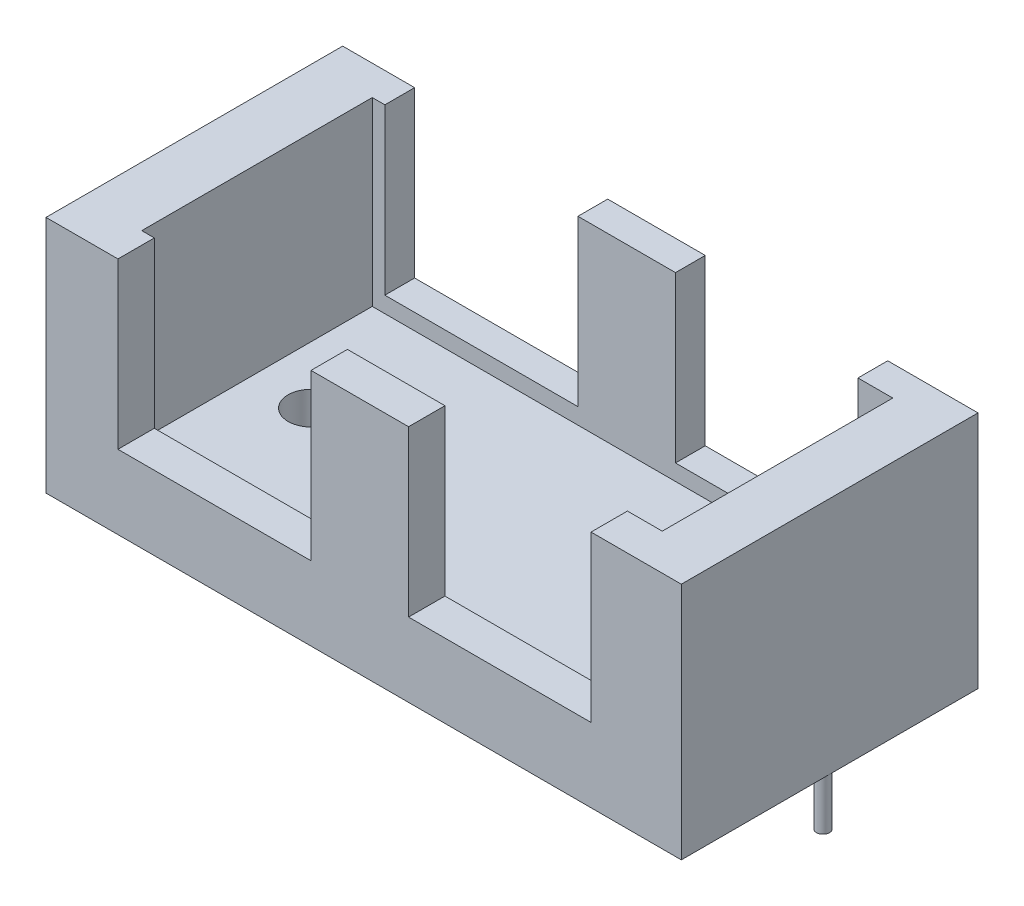
SolidWorks part; units mm, degrees
ref_plane "Front Plane" through (0, 0, 0) normal (0, 0, 1) x (1, 0, 0)
ref_plane "Top Plane" through (0, 0, 0) normal (0, 1, 0) x (1, 0, 0)
ref_plane "Right Plane" through (0, 0, 0) normal (1, 0, 0) x (0, 0, -1)
sketch "Sketch1" plane through (0, 0, 0) normal (0, 1, 0) x (1, 0, 0)
  line L1 (-22.6748, 9.2149) -> (21.2252, 9.2149)
  line L2 (-22.6748, 9.2149) -> (-22.6748, -11.2851)
  line L3 (-22.6748, -11.2851) -> (21.2252, -11.2851)
  line L4 (21.2252, 9.2149) -> (21.2252, -11.2851)
  dimension "D1" = 43.9
  dimension "D2" = 20.5
extrude "Boss-Extrude1" add sketch "Sketch1" along normal blind 16.5
sketch "Sketch3" plane through (0, 0, 0) normal (0, -1, 0) x (-1, 0, 0)
  circle A0 centre (-13.1452, -1.0351) radius 1.6
  circle A1 centre (14.5948, -1.0351) radius 1.6
  dimension "D1" = 3.2
  dimension "D3" = 3.2
  dimension "D2" = 8.08
  dimension "D4" = 8.08
  dimension "D5" = 10.25
  dimension "D6" = 10.25
extrude "Cut-Extrude1" cut sketch "Sketch3" against normal blind 6.5
sketch "Sketch4" plane through (0, 0, -9.2149) normal (0, 0, -1) x (-1, 0, 0)
  line L1 (-14.9871, 20.7572) -> (-2.3784, 20.7572)
  line L2 (-14.9871, 20.7572) -> (-14.9871, 5.1077)
  line L3 (-14.9871, 5.1077) -> (-2.3784, 5.1077)
  line L4 (-2.3784, 20.7572) -> (-2.3784, 5.1077)
  line L5 (4.3623, 20.7572) -> (17.7032, 20.7572)
  line L6 (4.3623, 20.7572) -> (4.3623, 5.1077)
  line L7 (4.3623, 5.1077) -> (17.7032, 5.1077)
  line L8 (17.7032, 20.7572) -> (17.7032, 5.1077)
sketch "Sketch5" plane through (0, 16.5, 0) normal (0, 1, 0) x (1, 0, 0)
  line L1 (17.3922, -8.7709) -> (-18.5743, -8.7709)
  line L2 (17.3922, -8.7709) -> (17.3922, 7.159)
  line L3 (17.3922, 7.159) -> (-18.5743, 7.159)
  line L4 (-18.5743, -8.7709) -> (-18.5743, 7.159)
extrude "Cut-Extrude3" cut sketch "Sketch5" against normal blind 12.5
extrude "Cut-Extrude4" cut sketch "Sketch4" against normal blind 28.5
sketch "Sketch6" plane through (0, 0, 0) normal (0, -1, 0) x (1, 0, 0)
  circle A0 centre (20.7652, 1.0351) radius 0.45
  circle A1 centre (13.1452, 1.0351) radius 1.6 construction
  circle A2 centre (-22.2148, 1.0351) radius 0.45
  circle A3 centre (-14.5948, 1.0351) radius 1.6 construction
  dimension "D1" = 0.9
  dimension "D4" = 0.9
  dimension "D5" = 7.62
  dimension "D2" = 7.62
  dimension "D3" = 10.25
  dimension "D6" = 10.25
extrude "Boss-Extrude2" add sketch "Sketch6" along normal blind 3.5
